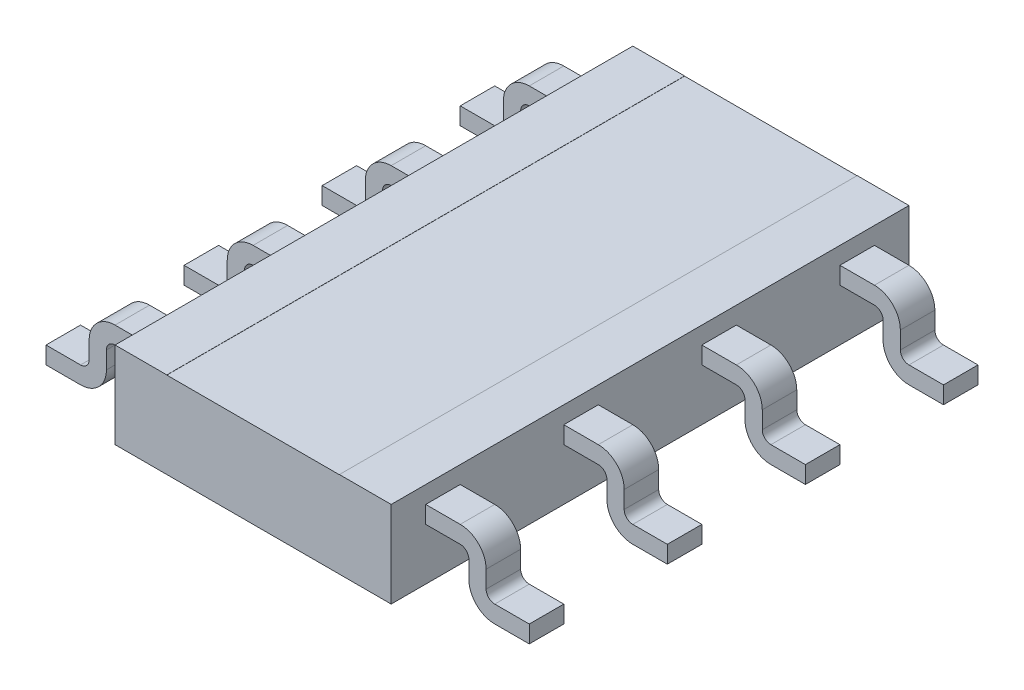
SolidWorks part; units mm, degrees
ref_plane "Front Plane" through (0, 0, 0) normal (0, 0, 1) x (1, 0, 0)
ref_plane "Top Plane" through (0, 0, 0) normal (0, 1, 0) x (1, 0, 0)
ref_plane "Right Plane" through (0, 0, 0) normal (1, 0, 0) x (0, 0, -1)
sketch "BaseS" plane through (0, 0, 0) normal (0, 1, 0) x (1, 0, 0)
  line L1 (-0.8, 1.5) -> (0.8, 1.5)
  line L2 (-0.8, 1.5) -> (-0.8, -1.5)
  line L3 (-0.8, -1.5) -> (0.8, -1.5)
  line L4 (0.8, 1.5) -> (0.8, -1.5)
  line L5 (-0.8, 1.5) -> (0.8, -1.5) construction
  line L6 (-0.8, -1.5) -> (0.8, 1.5) construction
  point P0 (0, 0)
  dimension "Length" = 3
  dimension "Width" = 1.6
extrude "Base" add sketch "BaseS" along normal mid plane 0.5
ref_plane "LegRP" through (0, 0, 1.2) normal (0, 0, 1) x (1, 0, 0)
sketch "MiddleLegS" plane through (0, 0, 1.2) normal (0, 0, 1) x (1, 0, 0)
  line L0 (0.8, 0.25) -> (0.8, -0.25) construction
  line L1 (-0.8, -0.25) -> (0.8, -0.25) construction
  line L3 (1.4, -0.2) -> (1.2, -0.2)
  line L4 (1.1, -0.1) -> (1.1, 0)
  line L5 (0.8, 0.1) -> (1, 0.1)
  line L6 (0.8, 0.25) -> (0.8, -0.25) construction
  arc A2 (1.1, -0.1) -> (1.2, -0.2) centre (1.2, -0.1) ccw
  arc A3 (1.1, 0) -> (1, 0.1) centre (1, 0) ccw
  dimension "D3" = 0.1
  dimension "D4" = 0.1
  dimension "D1" = 0.2
  dimension "D2" = 0.2
  dimension "D5" = 0.05
  dimension "Height" = 0.3
extrude "MiddleLeg" add sketch "MiddleLegS" along normal mid plane 0.2 thin contours L5 A3 L4 A2 L3 thin type mid plane wall 0.1
pattern_linear "LPattern1" count 4 spacing 0.8 along (0, 0, -1) of "MiddleLeg"
mirror "Mirror1" about plane through (0, 0, 0) normal (1, 0, 0) of "LPattern1", "MiddleLeg"
sketch "TextCutS" plane through (0, 0.25, 0) normal (0, 1, 0) x (1, 0, 0)
  line L0 (-0.8, -1.5) -> (0.8, -1.5) construction
  line L1 (-0.5, 1.5) -> (0.5, 1.5)
  line L2 (-0.5, 1.5) -> (-0.5, -1.5)
  line L3 (-0.5, -1.5) -> (0.5, -1.5)
  line L4 (0.5, 1.5) -> (0.5, -1.5)
  line L5 (-0.5, 1.5) -> (0.5, -1.5) construction
  line L6 (-0.5, -1.5) -> (0.5, 1.5) construction
  line L7 (-0.8, 1.5) -> (-0.8, -1.5) construction
  point P0 (0, 0)
  dimension "XDim" = 0.3
extrude "TextCut" cut sketch "TextCutS" against normal blind 0.001
